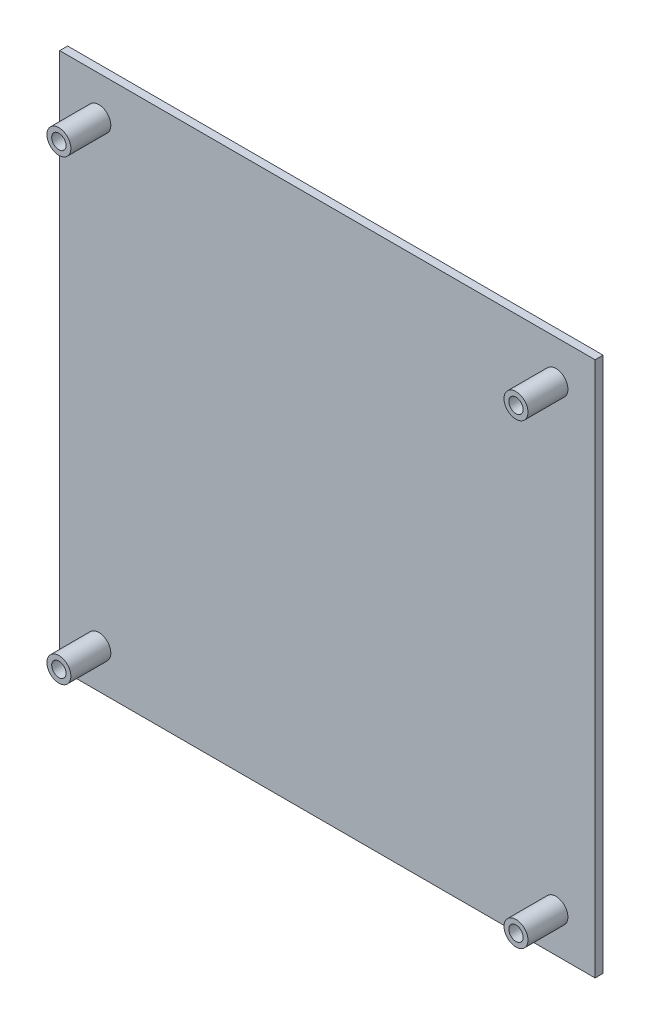
SolidWorks part; units mm, degrees
ref_plane "Plan de face" through (0, 0, 0) normal (0, 0, 1) x (1, 0, 0)
ref_plane "Plan de dessus" through (0, 0, 0) normal (0, 1, 0) x (1, 0, 0)
ref_plane "Plan de droite" through (0, 0, 0) normal (1, 0, 0) x (0, 0, -1)
sketch "Esquisse1" plane through (0, 0, 0) normal (0, 0, 1) x (1, 0, 0)
  line L1 (-67, 67) -> (67, 67)
  line L2 (-67, 67) -> (-67, -67)
  line L3 (-67, -67) -> (67, -67)
  line L4 (67, 67) -> (67, -67)
  line L5 (-67, 67) -> (67, -67) construction
  line L6 (-67, -67) -> (67, 67) construction
  point P0 (0, 0)
extrude "Boss.-Extru.1" add sketch "Esquisse1" along normal blind 5
sketch "Esquisse5" plane through (0, 0, 0) normal (0, 0, 1) x (1, 0, 0)
  line L2 (-67, 67) -> (67, 67)
  line L3 (-67, 67) -> (-67, -67)
  line L5 (-67, -67) -> (67, -67)
  line L7 (67, 67) -> (67, -67)
  line L8 (63, 63) -> (-63, 63)
  line L9 (63, 63) -> (63, -63)
  line L10 (63, -63) -> (-63, -63)
  line L11 (-63, 63) -> (-63, -63)
extrude "Enlèv. mat.-Extru.1" cut sketch "Esquisse5" along normal blind 3
sketch "Esquisse6" plane through (0, 0, 0) normal (0, 0, 1) x (1, 0, 0)
  circle A0 centre (57.2, 57.2) radius 1.8
  circle A1 centre (57.2, -57.2) radius 1.8
  circle A2 centre (-57.2, -57.2) radius 1.8
  circle A3 centre (-57.2, 57.2) radius 1.8
extrude "Enlèv. mat.-Extru.2" cut sketch "Esquisse6" along normal blind 6
sketch "Esquisse7" plane through (0, 0, 0) normal (0, 0, 1) x (1, 0, 0)
  circle A0 centre (57.2, 57.2) radius 1.8
  circle A1 centre (57.2, 57.2) radius 3
extrude "Boss.-Extru.2" add sketch "Esquisse7" along normal blind 15
sketch "Esquisse8" plane through (0, 0, 0) normal (0, 0, 1) x (1, 0, 0)
  circle A0 centre (-57.2, 57.2) radius 1.8
  circle A1 centre (-57.2, 57.2) radius 3
extrude "Boss.-Extru.3" add sketch "Esquisse8" along normal blind 15
sketch "Esquisse9" plane through (0, 0, 0) normal (0, 0, 1) x (1, 0, 0)
  circle A2 centre (-57.2, -57.2) radius 1.8
  circle A3 centre (-57.2, -57.2) radius 3
extrude "Boss.-Extru.6" add sketch "Esquisse9" along normal blind 15
sketch "Esquisse10" plane through (0, 0, 0) normal (0, 0, 1) x (1, 0, 0)
  circle A0 centre (57.2, -57.2) radius 1.8
  circle A1 centre (57.2, -57.2) radius 3
extrude "Boss.-Extru.7" add sketch "Esquisse10" along normal blind 15
